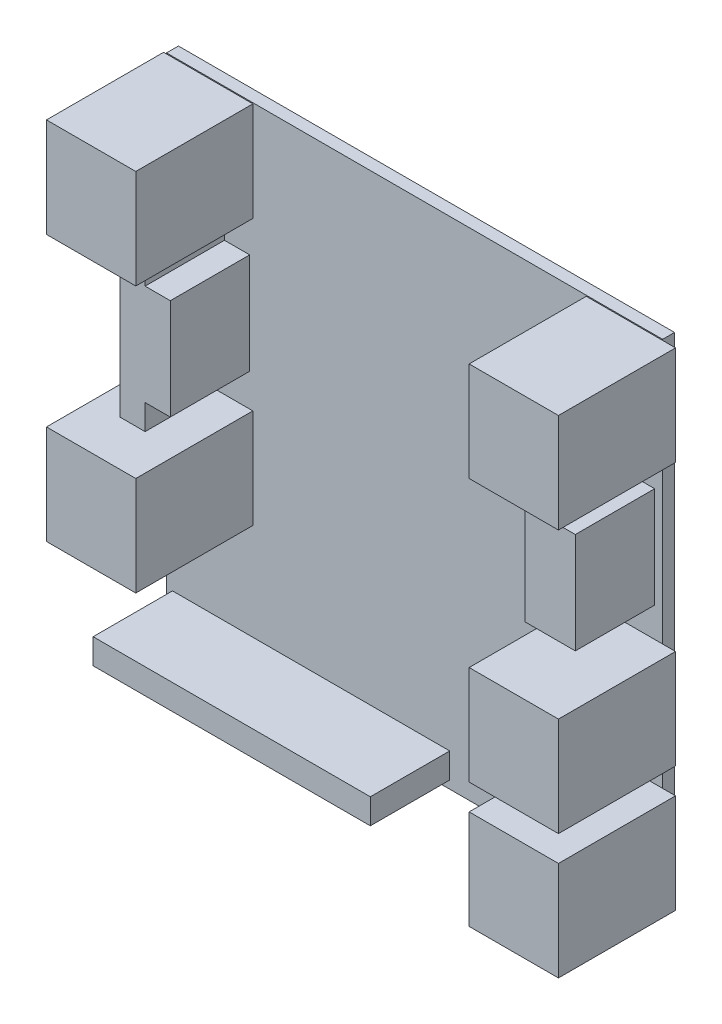
SolidWorks part; units mm, degrees
ref_plane "Alzado" through (0, 0, 0) normal (0, 0, 1) x (1, 0, 0)
ref_plane "Planta" through (0, 0, 0) normal (0, 1, 0) x (1, 0, 0)
ref_plane "Vista lateral" through (0, 0, 0) normal (1, 0, 0) x (0, 0, -1)
sketch "Croquis1" plane through (0, 0, 0) normal (0, 0, 1) x (1, 0, 0)
  line L1 (0, 0) -> (50, 0)
  line L2 (0, 0) -> (0, 50)
  line L3 (0, 50) -> (50, 50)
  line L4 (50, 0) -> (50, 50)
  dimension "D1" = 50
  dimension "D2" = 50
extrude "Saliente-Extruir1" add sketch "Croquis1" along normal blind 1.2
sketch "Croquis2" plane through (0, 0, 1.2) normal (0, 0, 1) x (1, 0, 0)
  line L0 (50, 50) -> (0, 50) construction
  line L1 (42.3, 0.8) -> (51.3, 0.8)
  line L2 (42.3, 0.8) -> (42.3, 10.8)
  line L3 (42.3, 10.8) -> (51.3, 10.8)
  line L4 (51.3, 0.8) -> (51.3, 10.8)
  line L5 (42.3, 13.4) -> (51.3, 13.4)
  line L6 (42.3, 13.4) -> (42.3, 23.4)
  line L7 (42.3, 23.4) -> (51.3, 23.4)
  line L8 (51.3, 13.4) -> (51.3, 23.4)
  line L9 (42.3, 39.9) -> (51.3, 39.9)
  line L10 (42.3, 39.9) -> (42.3, 49.9)
  line L11 (42.3, 49.9) -> (51.3, 49.9)
  line L12 (51.3, 39.9) -> (51.3, 49.9)
  line L13 (8.7, 49.9) -> (-0.3, 49.9)
  line L14 (8.7, 49.9) -> (8.7, 39.9)
  line L15 (8.7, 39.9) -> (-0.3, 39.9)
  line L16 (-0.3, 49.9) -> (-0.3, 39.9)
  line L17 (8.7, 23.1) -> (-0.3, 23.1)
  line L18 (8.7, 23.1) -> (8.7, 13.1)
  line L19 (8.7, 13.1) -> (-0.3, 13.1)
  line L20 (-0.3, 23.1) -> (-0.3, 13.1)
  line L21 (50, 0) -> (50, 50) construction
  line L22 (0, 50) -> (0, 0) construction
  dimension "D1" = 9
  dimension "D2" = 10
  dimension "D3" = 0.1
  dimension "D4" = 1.3
  dimension "D5" = 0.3
  dimension "D6" = 16.8
  dimension "D7" = 16.5
  dimension "D8" = 2.6
extrude "Saliente-Extruir2" add sketch "Croquis2" along normal blind 11.8
sketch "Croquis3" plane through (0, 0, 1.2) normal (0, 0, 1) x (1, 0, 0)
  line L0 (0, 39.9) -> (8.7, 39.9) construction
  line L1 (44.12, 36.56) -> (49.2, 36.56)
  line L2 (44.12, 36.56) -> (44.12, 26.4)
  line L3 (44.12, 26.4) -> (49.2, 26.4)
  line L4 (49.2, 36.56) -> (49.2, 26.4)
  line L5 (0.6, 3.34) -> (28.54, 3.34)
  line L6 (0.6, 3.34) -> (0.6, 0.8)
  line L7 (0.6, 0.8) -> (28.54, 0.8)
  line L8 (28.54, 3.34) -> (28.54, 0.8)
  line L9 (3.3, 39.1) -> (5.84, 39.1)
  line L10 (3.3, 39.1) -> (3.3, 23.86)
  line L11 (3.3, 23.86) -> (5.84, 23.86)
  line L12 (5.84, 39.1) -> (5.84, 23.86)
  line L13 (5.84, 36.56) -> (8.38, 36.56)
  line L14 (5.84, 36.56) -> (5.84, 26.4)
  line L15 (5.84, 26.4) -> (8.38, 26.4)
  line L16 (8.38, 36.56) -> (8.38, 26.4)
  line L17 (0, 39.9) -> (0, 23.1) construction
  line L18 (50, 23.4) -> (50, 39.9) construction
  line L19 (0, 0) -> (50, 0) construction
  line L20 (0, 13.1) -> (0, 0) construction
  dimension "D1" = 2.54
  dimension "D2" = 2.54
  dimension "D3" = 15.24
  dimension "D4" = 10.16
  dimension "D5" = 0.8
  dimension "D6" = 5.08
  dimension "D7" = 3.3
  dimension "D8" = 0.8
  dimension "D9" = 27.94
  dimension "D10" = 0.8
  dimension "D11" = 0.6
extrude "Saliente-Extruir3" add sketch "Croquis3" along normal blind 8 contours L8 L5 L6 L7 | L12 L9 L10 L11 | L16 L13 L12 L15 | L4 L1 L2 L3
